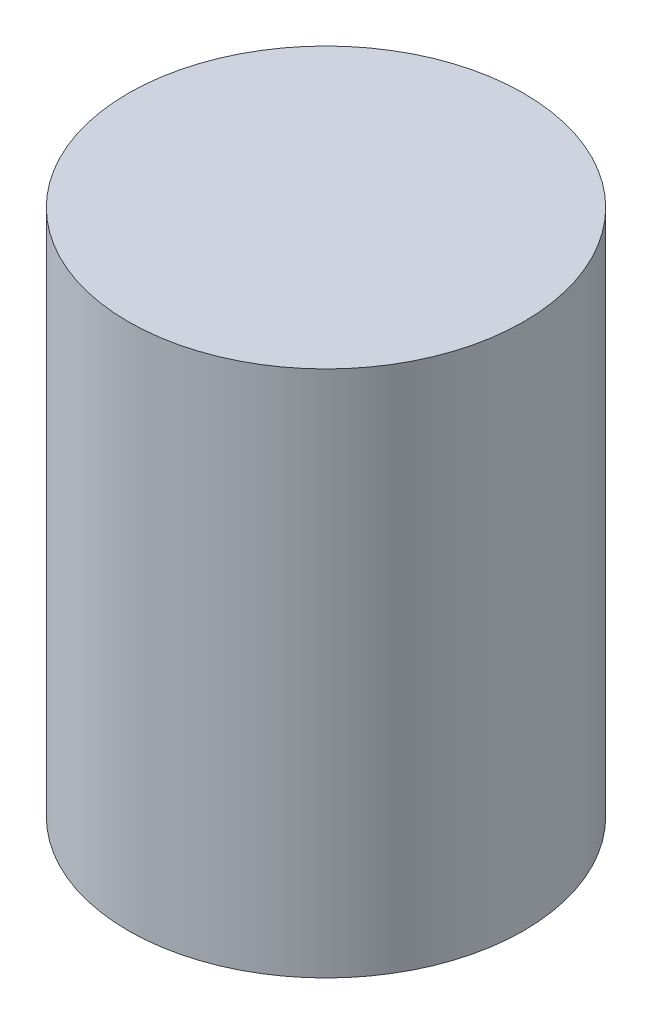
SolidWorks part; units mm, degrees
ref_plane "Plano frontal" through (0, 0, 0) normal (0, 0, 1) x (1, 0, 0)
ref_plane "Plano superior" through (0, 0, 0) normal (0, 1, 0) x (1, 0, 0)
ref_plane "Plano direito" through (0, 0, 0) normal (1, 0, 0) x (0, 0, -1)
sketch "Esboço1" plane through (0, 0, 0) normal (0, 0, 1) x (1, 0, 0)
  line L0 (0, 0) -> (0, 132.364) construction
  line L1 (0, 0) -> (79.4441, 0) construction
  line L2 (0, 80) -> (30, 80)
  line L3 (30, 80) -> (30, 0)
  line L4 (30, 0) -> (0, 0)
  line L5 (0, 0) -> (0, 80)
  dimension "D1" = 60
  dimension "D2" = 80
revolve "Revolução1" add sketch "Esboço1" angle 360 about L0
